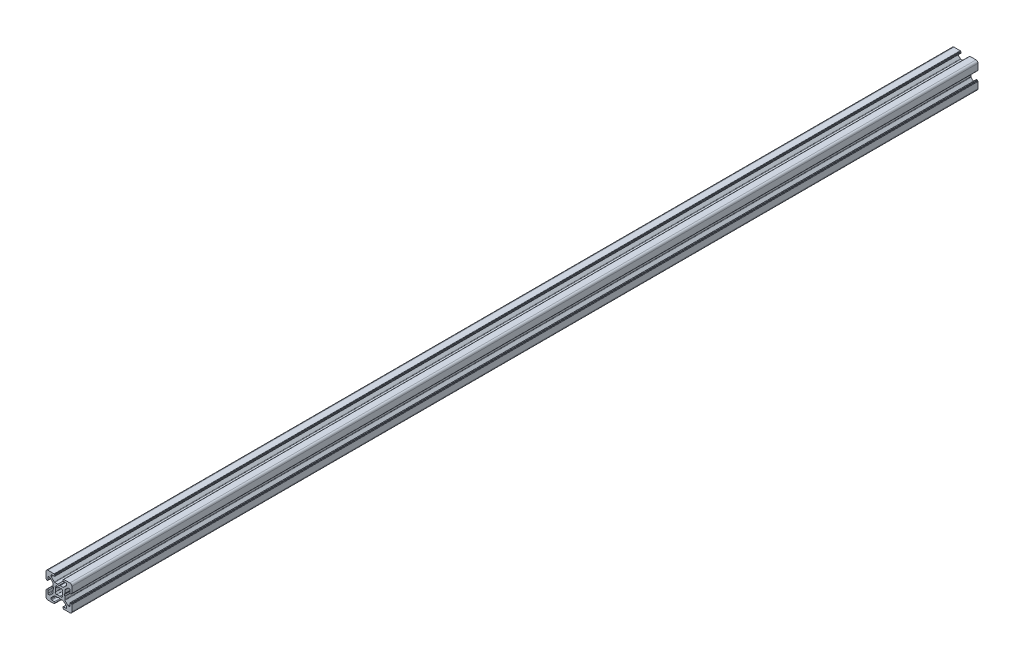
SolidWorks part; units mm, degrees
ref_plane "Płaszczyzna przednia" through (0, 0, 0) normal (0, 0, 1) x (1, 0, 0)
ref_plane "Płaszczyzna górna" through (0, 0, 0) normal (0, 1, 0) x (1, 0, 0)
ref_plane "Płaszczyzna prawa" through (0, 0, 0) normal (1, 0, 0) x (0, 0, -1)
sketch "Croquis" plane through (0, 0, 0) normal (0, 0, 1) x (1, 0, 0)
  line L0 (7.0078, -1.8401) -> (7.5547, -2.4918)
  line L1 (7.5547, -5.0082) -> (7.0078, -5.6599)
  line L2 (8.0861, -6.7396) -> (8.7418, -6.1953)
  line L3 (11.2582, -6.1953) -> (11.9139, -6.7396)
  line L4 (12.9922, -5.6599) -> (12.4453, -5.0082)
  line L5 (12.4453, -2.4918) -> (12.9922, -1.8401)
  line L6 (11.9139, -0.7604) -> (11.2582, -1.3047)
  line L7 (8.7418, -1.3047) -> (8.0861, -0.7604)
  line L8 (6.25, 6.25) -> (1.5, 6.25)
  line L9 (6.45, 5.95) -> (6.45, 6.05)
  line L10 (6.8, 5.75) -> (6.65, 5.75)
  line L11 (7, 5.25) -> (7, 5.55)
  line L12 (4.5, 4.75) -> (6.5, 4.75)
  line L13 (4, 3.5178) -> (4, 4.25)
  line L14 (6.4142, 0.8964) -> (4.1464, 3.1642)
  line L15 (9.0464, 0.75) -> (6.7678, 0.75)
  line L16 (9.9, 0.2881) -> (9.1464, 0.7232)
  line L17 (10.8536, 0.7232) -> (10.1, 0.2881)
  line L18 (13.2322, 0.75) -> (10.9536, 0.75)
  line L19 (15.8536, 3.1642) -> (13.5858, 0.8964)
  line L20 (16, 4.25) -> (16, 3.5178)
  line L21 (13.5, 4.75) -> (15.5, 4.75)
  line L22 (13, 5.55) -> (13, 5.25)
  line L23 (13.35, 5.75) -> (13.2, 5.75)
  line L24 (13.55, 6.05) -> (13.55, 5.95)
  line L25 (18.5, 6.25) -> (13.75, 6.25)
  line L26 (20, 0) -> (20, 4.75)
  line L27 (19.7, -0.2) -> (19.8, -0.2)
  line L28 (19.5, -0.55) -> (19.5, -0.4)
  line L29 (19, -0.75) -> (19.3, -0.75)
  line L30 (18.5, 1.75) -> (18.5, -0.25)
  line L31 (17.2678, 2.25) -> (18, 2.25)
  line L32 (14.6464, -0.1642) -> (16.9142, 2.1036)
  line L33 (14.5, -2.7964) -> (14.5, -0.5178)
  line L34 (14.0381, -3.65) -> (14.4732, -2.8964)
  line L35 (14.4732, -4.6036) -> (14.0381, -3.85)
  line L36 (14.5, -6.9822) -> (14.5, -4.7036)
  line L37 (16.9142, -9.6036) -> (14.6464, -7.3358)
  line L38 (18, -9.75) -> (17.2678, -9.75)
  line L39 (18.5, -7.25) -> (18.5, -9.25)
  line L40 (19.3, -6.75) -> (19, -6.75)
  line L41 (19.5, -7.1) -> (19.5, -6.95)
  line L42 (19.8, -7.3) -> (19.7, -7.3)
  line L43 (20, -12.25) -> (20, -7.5)
  line L44 (13.75, -13.75) -> (18.5, -13.75)
  line L45 (13.55, -13.45) -> (13.55, -13.55)
  line L46 (13.2, -13.25) -> (13.35, -13.25)
  line L47 (13, -12.75) -> (13, -13.05)
  line L48 (15.5, -12.25) -> (13.5, -12.25)
  line L49 (16, -11.0178) -> (16, -11.75)
  line L50 (13.5858, -8.3964) -> (15.8536, -10.6642)
  line L51 (10.9536, -8.25) -> (13.2322, -8.25)
  line L52 (10.1, -7.7881) -> (10.8536, -8.2232)
  line L53 (9.1464, -8.2232) -> (9.9, -7.7881)
  line L54 (6.7678, -8.25) -> (9.0464, -8.25)
  line L55 (4.1464, -10.6642) -> (6.4142, -8.3964)
  line L56 (4, -11.75) -> (4, -11.0178)
  line L57 (6.5, -12.25) -> (4.5, -12.25)
  line L58 (7, -13.05) -> (7, -12.75)
  line L59 (6.65, -13.25) -> (6.8, -13.25)
  line L60 (6.45, -13.55) -> (6.45, -13.45)
  line L61 (1.5, -13.75) -> (6.25, -13.75)
  line L62 (0, -7.5) -> (0, -12.25)
  line L63 (0.3, -7.3) -> (0.2, -7.3)
  line L64 (0.5, -6.95) -> (0.5, -7.1)
  line L65 (1, -6.75) -> (0.7, -6.75)
  line L66 (1.5, -9.25) -> (1.5, -7.25)
  line L67 (2.7322, -9.75) -> (2, -9.75)
  line L68 (5.3536, -7.3358) -> (3.0858, -9.6036)
  line L69 (5.5, -4.7036) -> (5.5, -6.9822)
  line L70 (5.9619, -3.85) -> (5.5268, -4.6036)
  line L71 (5.5268, -2.8964) -> (5.9619, -3.65)
  line L72 (5.5, -0.5178) -> (5.5, -2.7964)
  line L73 (3.0858, 2.1036) -> (5.3536, -0.1642)
  line L74 (2, 2.25) -> (2.7322, 2.25)
  line L75 (1.5, -0.25) -> (1.5, 1.75)
  line L76 (0.7, -0.75) -> (1, -0.75)
  line L77 (0.5, -0.4) -> (0.5, -0.55)
  line L78 (0.2, -0.2) -> (0.3, -0.2)
  line L79 (0, 4.75) -> (0, 0)
  arc A0 (7.5547, -2.4918) -> (7.5547, -5.0082) centre (10, -3.75) ccw
  arc A1 (7.0078, -5.6599) -> (8.0861, -6.7396) centre (10, -3.75) ccw
  arc A2 (8.7418, -6.1953) -> (11.2582, -6.1953) centre (10, -3.75) ccw
  arc A3 (11.9139, -6.7396) -> (12.9922, -5.6599) centre (10, -3.75) ccw
  arc A4 (12.4453, -5.0082) -> (12.4453, -2.4918) centre (10, -3.75) ccw
  arc A5 (12.9922, -1.8401) -> (11.9139, -0.7604) centre (10, -3.75) ccw
  arc A6 (11.2582, -1.3047) -> (8.7418, -1.3047) centre (10, -3.75) ccw
  arc A7 (8.0861, -0.7604) -> (7.0078, -1.8401) centre (10, -3.75) ccw
  arc A8 (6.45, 6.05) -> (6.25, 6.25) centre (6.25, 6.05) ccw
  arc A9 (6.45, 5.95) -> (6.65, 5.75) centre (6.65, 5.95) ccw
  arc A10 (7, 5.55) -> (6.8, 5.75) centre (6.8, 5.55) ccw
  arc A11 (6.5, 4.75) -> (7, 5.25) centre (6.5, 5.25) ccw
  arc A12 (4.5, 4.75) -> (4, 4.25) centre (4.5, 4.25) ccw
  arc A13 (4, 3.5178) -> (4.1464, 3.1642) centre (4.5, 3.5178) ccw
  arc A14 (6.4142, 0.8964) -> (6.7678, 0.75) centre (6.7678, 1.25) ccw
  arc A15 (9.1464, 0.7232) -> (9.0464, 0.75) centre (9.0464, 0.55) ccw
  arc A16 (9.9, 0.2881) -> (10.1, 0.2881) centre (10, 0.4613) ccw
  arc A17 (10.9536, 0.75) -> (10.8536, 0.7232) centre (10.9536, 0.55) ccw
  arc A18 (13.2322, 0.75) -> (13.5858, 0.8964) centre (13.2322, 1.25) ccw
  arc A19 (15.8536, 3.1642) -> (16, 3.5178) centre (15.5, 3.5178) ccw
  arc A20 (16, 4.25) -> (15.5, 4.75) centre (15.5, 4.25) ccw
  arc A21 (13, 5.25) -> (13.5, 4.75) centre (13.5, 5.25) ccw
  arc A22 (13.2, 5.75) -> (13, 5.55) centre (13.2, 5.55) ccw
  arc A23 (13.35, 5.75) -> (13.55, 5.95) centre (13.35, 5.95) ccw
  arc A24 (13.75, 6.25) -> (13.55, 6.05) centre (13.75, 6.05) ccw
  arc A25 (20, 4.75) -> (18.5, 6.25) centre (18.5, 4.75) ccw
  arc A26 (19.8, -0.2) -> (20, 0) centre (19.8, 0) ccw
  arc A27 (19.7, -0.2) -> (19.5, -0.4) centre (19.7, -0.4) ccw
  arc A28 (19.3, -0.75) -> (19.5, -0.55) centre (19.3, -0.55) ccw
  arc A29 (18.5, -0.25) -> (19, -0.75) centre (19, -0.25) ccw
  arc A30 (18.5, 1.75) -> (18, 2.25) centre (18, 1.75) ccw
  arc A31 (17.2678, 2.25) -> (16.9142, 2.1036) centre (17.2678, 1.75) ccw
  arc A32 (14.6464, -0.1642) -> (14.5, -0.5178) centre (15, -0.5178) ccw
  arc A33 (14.4732, -2.8964) -> (14.5, -2.7964) centre (14.3, -2.7964) ccw
  arc A34 (14.0381, -3.65) -> (14.0381, -3.85) centre (14.2113, -3.75) ccw
  arc A35 (14.5, -4.7036) -> (14.4732, -4.6036) centre (14.3, -4.7036) ccw
  arc A36 (14.5, -6.9822) -> (14.6464, -7.3358) centre (15, -6.9822) ccw
  arc A37 (16.9142, -9.6036) -> (17.2678, -9.75) centre (17.2678, -9.25) ccw
  arc A38 (18, -9.75) -> (18.5, -9.25) centre (18, -9.25) ccw
  arc A39 (19, -6.75) -> (18.5, -7.25) centre (19, -7.25) ccw
  arc A40 (19.5, -6.95) -> (19.3, -6.75) centre (19.3, -6.95) ccw
  arc A41 (19.5, -7.1) -> (19.7, -7.3) centre (19.7, -7.1) ccw
  arc A42 (20, -7.5) -> (19.8, -7.3) centre (19.8, -7.5) ccw
  arc A43 (18.5, -13.75) -> (20, -12.25) centre (18.5, -12.25) ccw
  arc A44 (13.55, -13.55) -> (13.75, -13.75) centre (13.75, -13.55) ccw
  arc A45 (13.55, -13.45) -> (13.35, -13.25) centre (13.35, -13.45) ccw
  arc A46 (13, -13.05) -> (13.2, -13.25) centre (13.2, -13.05) ccw
  arc A47 (13.5, -12.25) -> (13, -12.75) centre (13.5, -12.75) ccw
  arc A48 (15.5, -12.25) -> (16, -11.75) centre (15.5, -11.75) ccw
  arc A49 (16, -11.0178) -> (15.8536, -10.6642) centre (15.5, -11.0178) ccw
  arc A50 (13.5858, -8.3964) -> (13.2322, -8.25) centre (13.2322, -8.75) ccw
  arc A51 (10.8536, -8.2232) -> (10.9536, -8.25) centre (10.9536, -8.05) ccw
  arc A52 (10.1, -7.7881) -> (9.9, -7.7881) centre (10, -7.9613) ccw
  arc A53 (9.0464, -8.25) -> (9.1464, -8.2232) centre (9.0464, -8.05) ccw
  arc A54 (6.7678, -8.25) -> (6.4142, -8.3964) centre (6.7678, -8.75) ccw
  arc A55 (4.1464, -10.6642) -> (4, -11.0178) centre (4.5, -11.0178) ccw
  arc A56 (4, -11.75) -> (4.5, -12.25) centre (4.5, -11.75) ccw
  arc A57 (7, -12.75) -> (6.5, -12.25) centre (6.5, -12.75) ccw
  arc A58 (6.8, -13.25) -> (7, -13.05) centre (6.8, -13.05) ccw
  arc A59 (6.65, -13.25) -> (6.45, -13.45) centre (6.65, -13.45) ccw
  arc A60 (6.25, -13.75) -> (6.45, -13.55) centre (6.25, -13.55) ccw
  arc A61 (0, -12.25) -> (1.5, -13.75) centre (1.5, -12.25) ccw
  arc A62 (0.2, -7.3) -> (0, -7.5) centre (0.2, -7.5) ccw
  arc A63 (0.3, -7.3) -> (0.5, -7.1) centre (0.3, -7.1) ccw
  arc A64 (0.7, -6.75) -> (0.5, -6.95) centre (0.7, -6.95) ccw
  arc A65 (1.5, -7.25) -> (1, -6.75) centre (1, -7.25) ccw
  arc A66 (1.5, -9.25) -> (2, -9.75) centre (2, -9.25) ccw
  arc A67 (2.7322, -9.75) -> (3.0858, -9.6036) centre (2.7322, -9.25) ccw
  arc A68 (5.3536, -7.3358) -> (5.5, -6.9822) centre (5, -6.9822) ccw
  arc A69 (5.5268, -4.6036) -> (5.5, -4.7036) centre (5.7, -4.7036) ccw
  arc A70 (5.9619, -3.85) -> (5.9619, -3.65) centre (5.7887, -3.75) ccw
  arc A71 (5.5, -2.7964) -> (5.5268, -2.8964) centre (5.7, -2.7964) ccw
  arc A72 (5.5, -0.5178) -> (5.3536, -0.1642) centre (5, -0.5178) ccw
  arc A73 (3.0858, 2.1036) -> (2.7322, 2.25) centre (2.7322, 1.75) ccw
  arc A74 (2, 2.25) -> (1.5, 1.75) centre (2, 1.75) ccw
  arc A75 (1, -0.75) -> (1.5, -0.25) centre (1, -0.25) ccw
  arc A76 (0.5, -0.55) -> (0.7, -0.75) centre (0.7, -0.55) ccw
  arc A77 (0.5, -0.4) -> (0.3, -0.2) centre (0.3, -0.4) ccw
  arc A78 (0, 0) -> (0.2, -0.2) centre (0.2, 0) ccw
  arc A79 (1.5, 6.25) -> (0, 4.75) centre (1.5, 4.75) ccw
  dimension "D4" = 2.75
  dimension "D1" = 20
  dimension "D2" = 20
  dimension "D3" = 6
extrude "Saliente_Extruir" add sketch "Croquis" along normal blind 700
